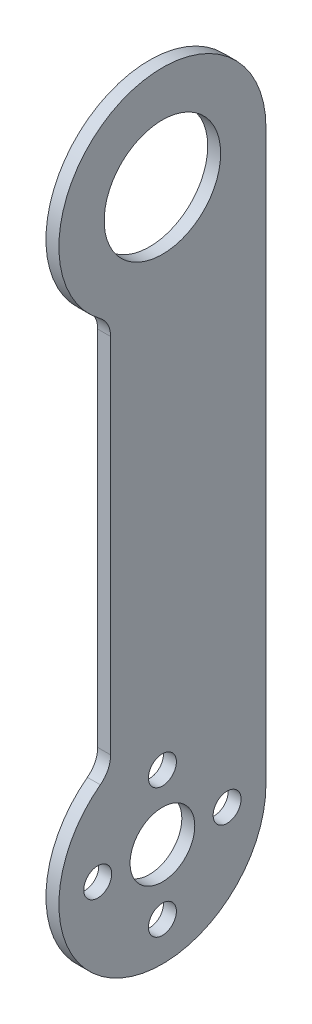
SolidWorks part; units mm, degrees
ref_plane "Front Plane" through (0, 0, 0) normal (0, 0, 1) x (1, 0, 0)
ref_plane "Top Plane" through (0, 0, 0) normal (0, 1, 0) x (1, 0, 0)
ref_plane "Right Plane" through (0, 0, 0) normal (1, 0, 0) x (0, 0, -1)
sketch "Sketch1" plane through (0, 0, 0) normal (1, 0, 0) x (0, 0, -1)
  line L0 (0, 55) -> (0, -55) construction
  line L1 (0, 0) -> (0, 139.7) construction
  line L2 (0, 0) -> (0, 15.875) construction
  line L4 (25.4, 139.7) -> (25.4, 0)
  line L6 (-12.7, 114.3) -> (-12.7, 25.4)
  circle A0 centre (0, 0) radius 7.9375
  circle A1 centre (0, 139.7) radius 14.2875
  circle A2 centre (0, 0) radius 15.875 construction
  circle A3 centre (0, 15.875) radius 3.429
  circle A4 centre (15.875, 0) radius 3.429
  circle A5 centre (0, -15.875) radius 3.429
  circle A6 centre (-15.875, 0) radius 3.429
  arc A7 (25.4, 139.7) -> (-15.24, 119.38) centre (0, 139.7) ccw
  arc A8 (-15.24, 20.32) -> (25.4, 0) centre (0, 0) ccw
  arc A9 (-12.7, 25.4) -> (-15.24, 20.32) centre (-19.05, 25.4) cw
  arc A10 (-12.7, 114.3) -> (-15.24, 119.38) centre (-19.05, 114.3) ccw
  point P10 (-10.688, 95.4472)
  point P11 (0, 0)
  point P24 (-25.4, 115.8875)
  point P25 (25.4, 0)
  point P27 (0, 0)
  point P28 (-25.4, 115.8875)
  point P29 (-10.6894, 92.8456)
  point P30 (0, 0)
  point P31 (-10.688, 23.0573)
  point P32 (-10.6547, 22.056)
  dimension "D1" = 15.875
  dimension "D3" = 28.575
  dimension "D4" = 31.75
  dimension "D5" = 6.858
  dimension "D8" = 50.8
  dimension "D11" = 6.35
  dimension "D2" = 139.7
  dimension "D7" = 15.875
  dimension "D9" = 12.7
  dimension "D6" = 4
extrude "Boss-Extrude1" add sketch "Sketch1" along normal blind 3.175
